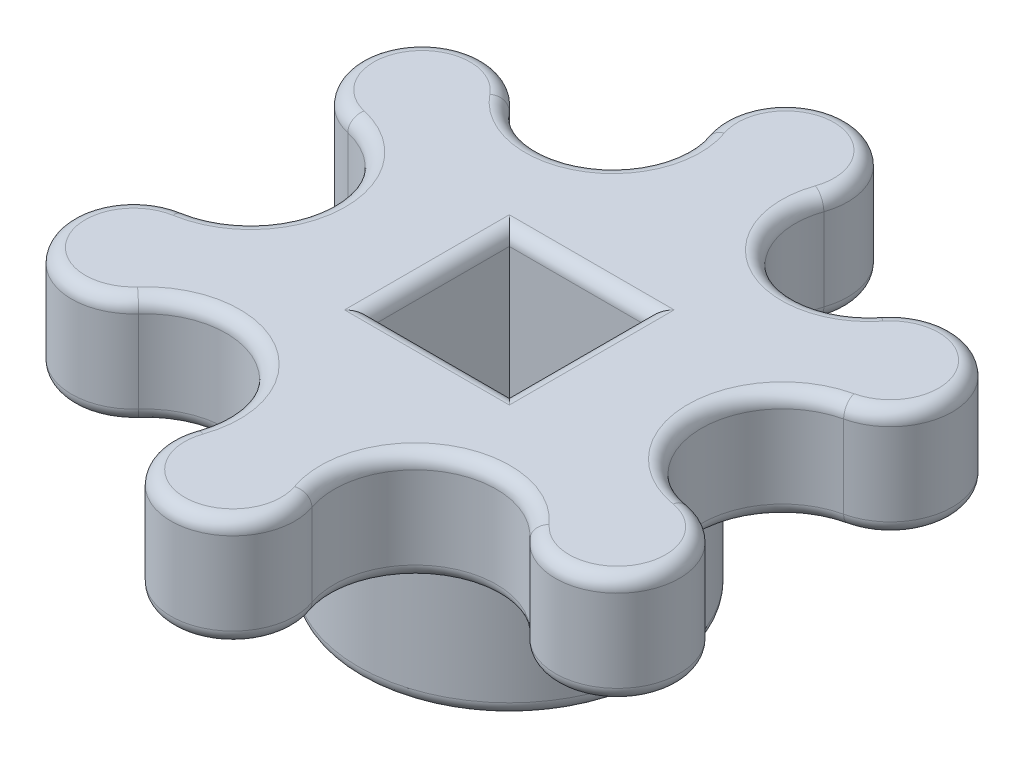
SolidWorks part; units mm, degrees
ref_plane "Plan de face" through (0, 0, 0) normal (0, 0, 1) x (1, 0, 0)
ref_plane "Plan de dessus" through (0, 0, 0) normal (0, 1, 0) x (1, 0, 0)
ref_plane "Plan de droite" through (0, 0, 0) normal (1, 0, 0) x (0, 0, -1)
sketch "Esquisse1" plane through (0, 0, 0) normal (0, 1, 0) x (1, 0, 0)
  line L0 (0, 0) -> (0, 10.0632) construction
  line L2 (-2.5, 2.5) -> (2.5, 2.5)
  line L3 (-2.5, 2.5) -> (-2.5, -2.5)
  line L4 (-2.5, -2.5) -> (2.5, -2.5)
  line L5 (2.5, 2.5) -> (2.5, -2.5)
  line L6 (-2.5, 2.5) -> (2.5, -2.5) construction
  line L7 (-2.5, -2.5) -> (2.5, 2.5) construction
  circle A0 centre (0, 0) radius 12.3207 construction
  arc A1 (2.131, 9.3178) -> (-2.131, 9.3178) centre (0, 10.0632) ccw
  arc A2 (2.131, 9.3178) -> (6.7622, 6.7554) centre (4.6651, 8.4315) ccw
  circle A3 centre (0, 0) radius 9.5584 construction
  arc A4 (9.0264, 3.1446) -> (9.1847, -2.6464) centre (9.6812, 0.2648) ccw
  arc A5 (9.0264, 3.1446) -> (6.7622, 6.7554) centre (8.5257, 5.3459) ccw
  arc A6 (7.1214, -6.3756) -> (2.131, -9.3178) centre (4.9187, -8.3428) ccw
  arc A7 (7.1214, -6.3756) -> (9.1847, -2.6464) centre (8.8052, -4.8719) ccw
  arc A8 (-2.131, -9.3178) -> (-7.1214, -6.3756) centre (-4.9187, -8.3428) ccw
  arc A9 (-2.131, -9.3178) -> (2.131, -9.3178) centre (0, -10.0632) ccw
  arc A10 (-9.1847, -2.6464) -> (-9.0264, 3.1446) centre (-9.6812, 0.2648) ccw
  arc A11 (-9.1847, -2.6464) -> (-7.1214, -6.3756) centre (-8.8052, -4.8719) ccw
  arc A12 (-6.7622, 6.7554) -> (-2.131, 9.3178) centre (-4.6651, 8.4315) ccw
  arc A13 (-6.7622, 6.7554) -> (-9.0264, 3.1446) centre (-8.5257, 5.3459) ccw
  point P9 (0, 0)
  point P37 (-0.0258, -0.0989)
  dimension "D1" = 24.6414
  dimension "D2" = 5
  dimension "D3" = 19.1168
  dimension "D4" = 5
extrude "Boss.-Extru.1" add sketch "Esquisse1" along normal blind 4
sketch "Esquisse2" plane through (0, 0, 0) normal (0, -1, 0) x (1, 0, 0)
  line L0 (2.5, -2.5) -> (-2.5, -2.5) construction
  line L1 (-2.5, -2.5) -> (-2.5, 2.5) construction
  line L2 (-2.5, 2.5) -> (2.5, 2.5) construction
  line L3 (2.5, 2.5) -> (2.5, -2.5) construction
  line L4 (2.5, -2.5) -> (-2.5, -2.5)
  line L5 (-2.5, -2.5) -> (-2.5, 2.5)
  line L6 (-2.5, 2.5) -> (2.5, 2.5)
  line L7 (2.5, 2.5) -> (2.5, -2.5)
  circle A0 centre (0, 0) radius 5.5
  dimension "D1" = 11
extrude "Boss.-Extru.2" add sketch "Esquisse2" along normal blind 5
fillet "Congé3" radius 0.5 21 edges at (0, 0, 5.5) (-3.3654, 0, -6.0825) (0, 0, -12.3207) (3.3654, 0, -6.0825) (10.4384, 0, -6.5452) (6.7291, 0, -0.1841) (10.7806, 0, 5.9648) (3.4188, 0, 5.7988) (0, 0, 12.3207) (-3.4188, 0, 5.7988) (-10.7806, 0, 5.9648) (-6.7291, 0, -0.1841) (-10.4384, 0, -6.5452) (0, 4, -2.5) (2.5, 4, 0) (0, 4, 2.5) (-2.5, 4, 0) (0, -5, 2.5) (-2.5, -5, 0) (0, -5, -2.5) (2.5, -5, 0)
fillet "Congé1" radius 0.5 13 edges at (-3.4188, 4, 5.7988) (-10.7806, 4, 5.9648) (-6.7291, 4, -0.1841) (-10.4384, 4, -6.5452) (-3.3654, 4, -6.0825) (0, 4, -12.3207) (3.3654, 4, -6.0825) (10.4384, 4, -6.5452) (6.7291, 4, -0.1841) (10.7806, 4, 5.9648) (3.4188, 4, 5.7988) (0, 4, 12.3207) (0, -5, -5.5)
